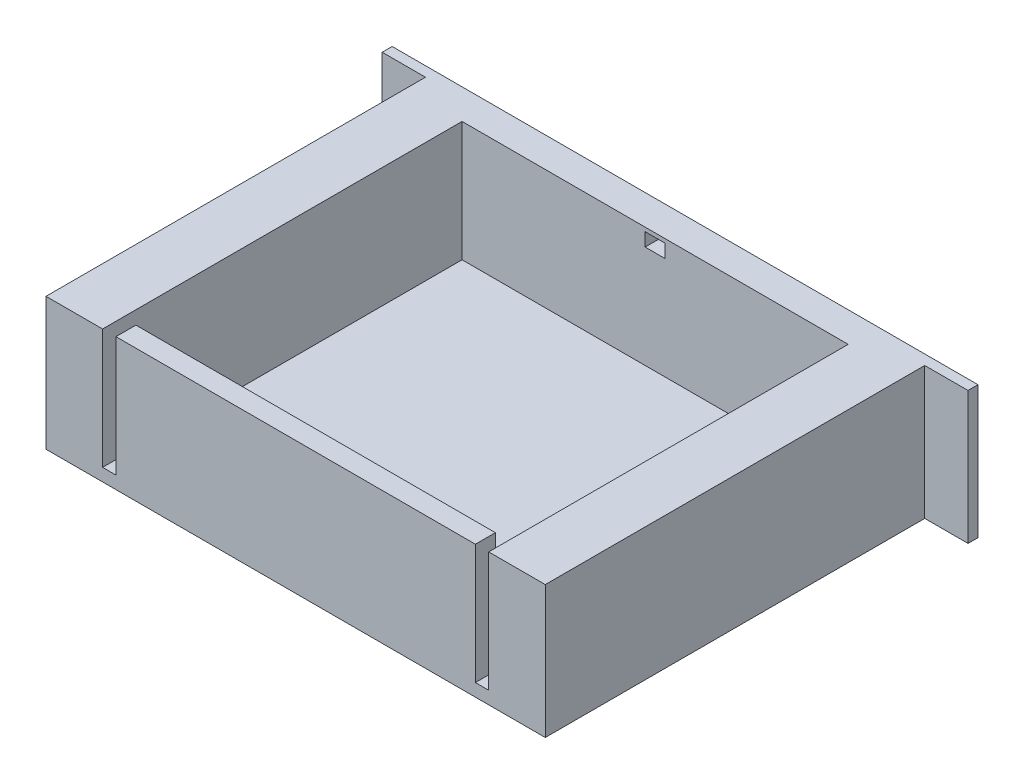
SolidWorks part; units mm, degrees
ref_plane "Płaszczyzna przednia" through (0, 0, 0) normal (0, 0, 1) x (1, 0, 0)
ref_plane "Płaszczyzna górna" through (0, 0, 0) normal (0, 1, 0) x (1, 0, 0)
ref_plane "Płaszczyzna prawa" through (0, 0, 0) normal (1, 0, 0) x (0, 0, -1)
sketch "Szkic1" plane through (0, 0, 0) normal (0, 0, 1) x (1, 0, 0)
  line L1 (0, 0) -> (-75, 0)
  line L2 (0, 0) -> (0, 19.9)
  line L3 (0, 19.9) -> (-75, 19.9)
  line L4 (-75, 0) -> (-75, 19.9)
  dimension "D1" = 19.9
  dimension "D2" = 75
extrude "Dodanie-wyciągnięcie1" add sketch "Szkic1" along normal blind 57
sketch "Szkic2" plane through (0, 0, 0) normal (0, 0, -1) x (-1, 0, 0)
  line L0 (0, 19.9) -> (75, 19.9) construction
  line L1 (-6.5, 19.9) -> (81.5, 19.9)
  line L2 (-6.5, 19.9) -> (-6.5, 0)
  line L3 (-6.5, 0) -> (81.5, 0)
  line L4 (81.5, 19.9) -> (81.5, 0)
  line L6 (75, 0) -> (0, 0) construction
  point P8 (37.5, 0)
  point P9 (37.5, 0)
  dimension "D1" = 88
extrude "Dodanie-wyciągnięcie2" add sketch "Szkic2" along normal blind 1.5
sketch "Szkic3" plane through (0, 19.9, 0) normal (0, 1, 0) x (1, 0, 0)
  line L1 (-8.5, -54) -> (-66.5, -54)
  line L2 (-8.5, -54) -> (-8.5, -3)
  line L3 (-8.5, -3) -> (-66.5, -3)
  line L4 (-66.5, -54) -> (-66.5, -3)
  line L5 (0, -57) -> (0, 0) construction
  line L6 (0, -57) -> (-75, -57) construction
  point P4 (-37.5, -54)
  point P7 (-37.5, -57)
  point P8 (-8.5, -28.5)
  point P11 (0, -28.5)
  dimension "D1" = 51
  dimension "D2" = 58
extrude "Wytnij-wyciągnięcie1" cut sketch "Szkic3" against normal blind 18
sketch "Szkic4" plane through (0, 19.9, 0) normal (0, 1, 0) x (1, 0, 0)
  line L0 (0, -57) -> (-75, -57) construction
  line L1 (-8.5, -54) -> (-10.5, -54)
  line L2 (-8.5, -54) -> (-8.5, -57)
  line L3 (-8.5, -57) -> (-10.5, -57)
  line L4 (-10.5, -54) -> (-10.5, -57)
  line L5 (-37.5, -57) -> (-37.5, 8.6092) construction
  line L10 (-64.5, -54) -> (-64.5, -57)
  line L11 (-66.5, -57) -> (-64.5, -57)
  line L12 (-66.5, -54) -> (-66.5, -57)
  line L13 (-66.5, -54) -> (-64.5, -54)
  dimension "D1" = 2
extrude "Wytnij-wyciągnięcie2" cut sketch "Szkic4" against normal up to surface (18 mm away) up to face at (-37.5, 1.9, 28.5)
sketch "Szkic5" plane through (0, 0, 0) normal (0, -1, 0) x (1, 0, 0)
  line L0 (6.5, -1.5) -> (-81.5, -1.5) construction
  line L1 (-30.0032, -1.5) -> (-32.5032, -1.5)
  line L2 (-42.5032, -1.5) -> (-45.0032, -1.5)
  arc A0 (-30.0032, -1.5) -> (-45.0032, -1.5) centre (-37.5032, -1.5) cw
  arc A1 (-32.5032, -1.5) -> (-42.5032, -1.5) centre (-37.5032, -1.5) cw
  point P6 (-37.5, -1.5)
  dimension "D2" = 5
  dimension "D1" = 15
extrude "Dodanie-wyciągnięcie3" add sketch "Szkic5" against normal blind 3 separate body
sketch "Szkic6" plane through (0, 0, -1.5) normal (0, 0, -1) x (-1, 0, 0)
  line L0 (81.5, 19.9) -> (-6.5, 19.9) construction
  line L1 (36, 19.3058) -> (39, 19.3058)
  line L2 (36, 19.3058) -> (36, 17.3058)
  line L3 (36, 17.3058) -> (39, 17.3058)
  line L4 (39, 19.3058) -> (39, 17.3058)
  point P4 (37.5, 17.3058)
  point P7 (37.5, 19.9)
  dimension "D1" = 3
  dimension "D2" = 2
extrude "Wytnij-wyciągnięcie3" cut sketch "Szkic6" against normal up to next (4.5 mm away)
